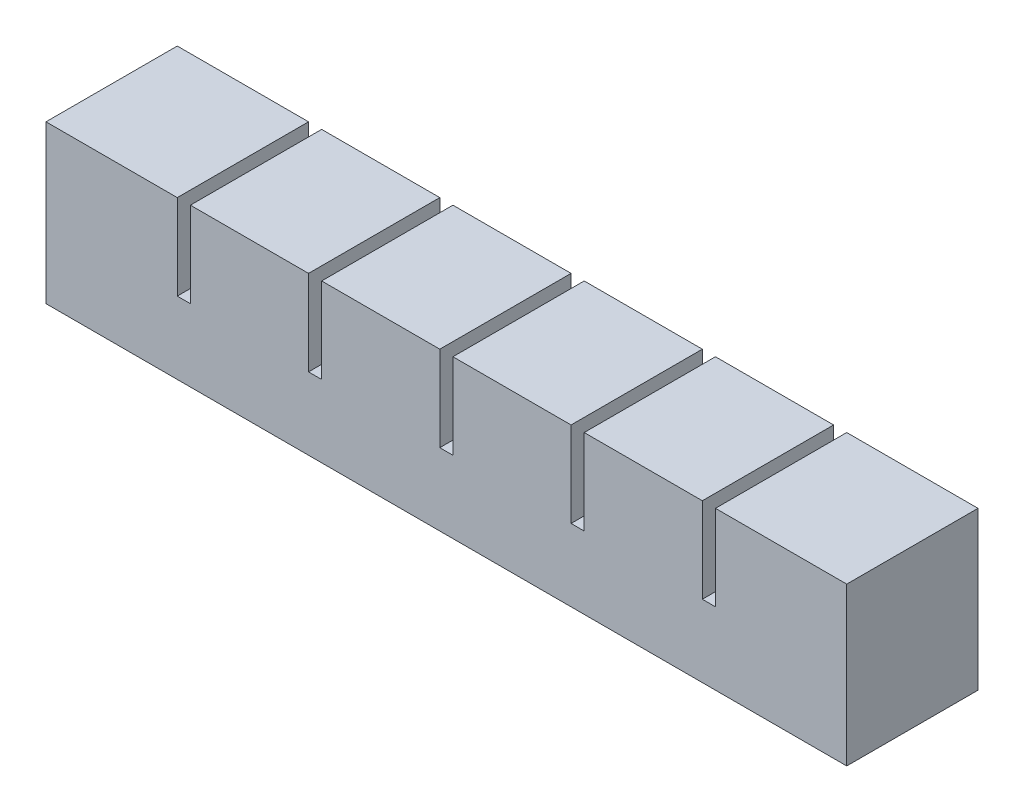
SolidWorks part; units mm, degrees
ref_plane "Front Plane" through (0, 0, 0) normal (0, 0, 1) x (1, 0, 0)
ref_plane "Top Plane" through (0, 0, 0) normal (0, 1, 0) x (1, 0, 0)
ref_plane "Right Plane" through (0, 0, 0) normal (1, 0, 0) x (0, 0, -1)
sketch "Sketch1" plane through (0, 0, 0) normal (0, 0, 1) x (1, 0, 0)
  line L1 (0, 0) -> (18, 0)
  line L2 (0, 0) -> (0, 18)
  line L3 (0, 18) -> (18, 18)
  line L4 (18, 0) -> (18, 18)
  dimension "D1" = 18
  dimension "D2" = 18
extrude "Boss-Extrude1" add sketch "Sketch1" along normal blind 20
sketch "Sketch2" plane through (0, 0, 0) normal (0, -1, 0) x (1, 0, 0)
  line L0 (18, 20) -> (18, 0) construction
  line L1 (5, 15) -> (13, 15)
  line L2 (5, 15) -> (5, 5)
  line L3 (5, 5) -> (13, 5)
  line L4 (13, 15) -> (13, 5)
  line L5 (0, 20) -> (18, 20) construction
  line L6 (0, 20) -> (0, 0) construction
  line L7 (0, 0) -> (18, 0) construction
  dimension "D1" = 5
  dimension "D2" = 5
  dimension "D3" = 5
  dimension "D4" = 5
extrude "Cut-Extrude1" cut sketch "Sketch2" against normal blind 13
sketch "Sketch3" plane through (18, 0, 0) normal (1, 0, 0) x (0, 0, -1)
  line L0 (0, 0) -> (0, 18) construction
  line L1 (-20, 0) -> (0, 0)
  line L2 (-20, 0) -> (-20, 5)
  line L3 (-20, 5) -> (0, 5)
  line L4 (0, 0) -> (0, 5)
  dimension "D1" = 5
extrude "Boss-Extrude2" add sketch "Sketch3" along normal blind 2
pattern_linear "LPattern1" count 6 spacing 20 along (1, 0, 0) of bodies 103
combine bodies "Combine1" operation type add bodies to combine 107 108 103 104 105 106
sketch "Sketch4" plane through (118, 0, 0) normal (1, 0, 0) x (0, 0, -1)
  line L1 (-20, 5) -> (0, 5)
  line L2 (-20, 5) -> (-20, 18)
  line L3 (-20, 18) -> (0, 18)
  line L4 (0, 5) -> (0, 18)
extrude "Boss-Extrude3" add sketch "Sketch4" along normal up to surface (2 mm away) up to face at (120, 2.5, 10)
sketch "Sketch5" plane through (0, 0, 0) normal (-1, 0, 0) x (0, 0, 1)
  line L1 (0, 18) -> (20, 18)
  line L2 (0, 18) -> (0, 0)
  line L3 (0, 0) -> (20, 0)
  line L4 (20, 18) -> (20, 0)
extrude "Boss-Extrude4" add sketch "Sketch5" along normal blind 2
ref_point "Point1"
sketch "Sketch6" plane through (0, 0, 0) normal (0, -1, 0) x (-1, 0, 0)
  line L0 (-113, -5) -> (-113, -15) construction
  line L1 (-5, -9) -> (-113, -9)
  line L2 (-5, -9) -> (-5, -11)
  line L3 (-5, -11) -> (-113, -11)
  line L4 (-113, -9) -> (-113, -11)
  line L5 (-5, -9) -> (-113, -11) construction
  line L6 (-5, -11) -> (-113, -9) construction
  point P0 (-59, -10)
  dimension "D1" = 2
extrude "Cut-Extrude2" cut sketch "Sketch6" against normal blind 2
sketch "Sketch7" plane through (0, 0, 0) normal (0, -1, 0) x (1, 0, 0)
  line L1 (-2, 20) -> (120, 20)
  line L2 (-2, 20) -> (-2, 0)
  line L3 (-2, 0) -> (120, 0)
  line L4 (120, 20) -> (120, 0)
extrude "Boss-Extrude5" add sketch "Sketch7" along normal blind 6
